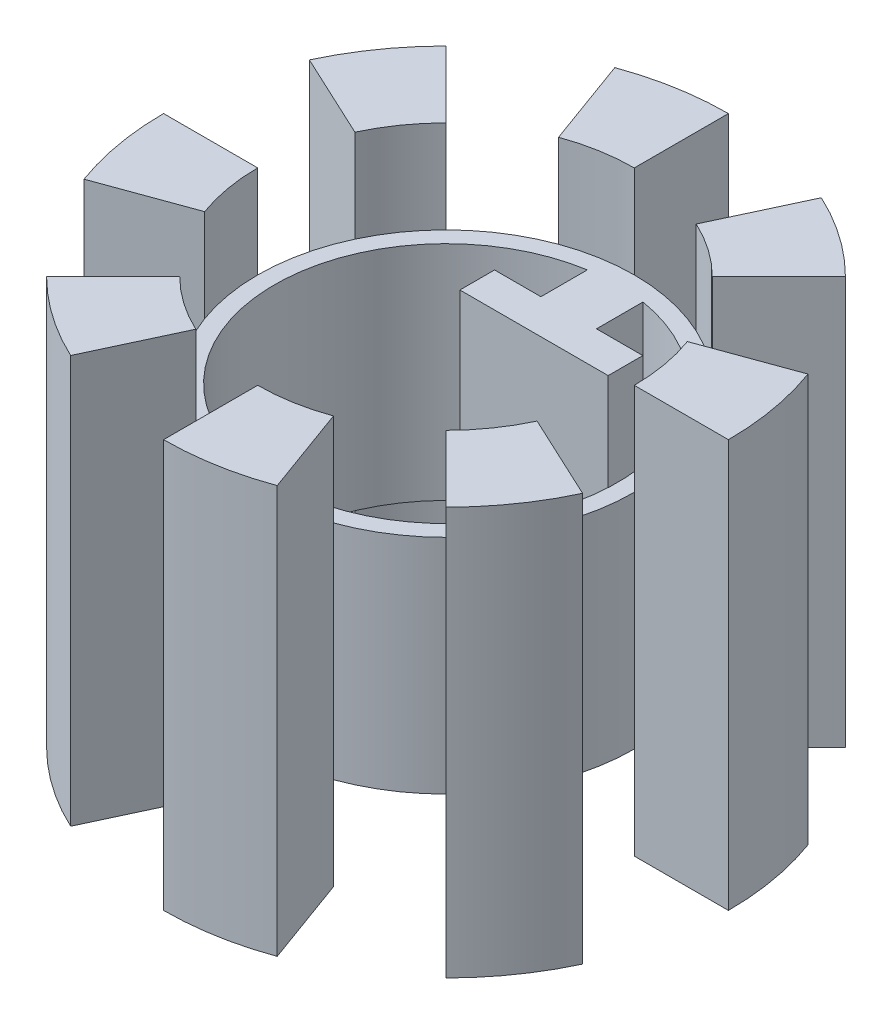
SolidWorks part; units mm, degrees
ref_plane "Front Plane" through (0, 0, 0) normal (0, 0, 1) x (1, 0, 0)
ref_plane "Top Plane" through (0, 0, 0) normal (0, 1, 0) x (1, 0, 0)
ref_plane "Right Plane" through (0, 0, 0) normal (1, 0, 0) x (0, 0, -1)
sketch "Sketch1" plane through (0, 0, 0) normal (0, 1, 0) x (1, 0, 0)
  line L0 (0, 15.24) -> (0, 0) construction
  line L1 (0, 0) -> (-5.2124, 14.3209) construction
  line L2 (0, 15.24) -> (0, 10.16)
  line L3 (-5.2124, 14.3209) -> (-3.4749, 9.5473)
  circle A0 centre (0, 0) radius 9.25
  arc A1 (0, 15.24) -> (-5.2124, 14.3209) centre (0, 0) ccw
  arc A2 (0, 10.16) -> (-3.4749, 9.5473) centre (0, 0) ccw
  circle A3 centre (0, 0) radius 10.16
  dimension "D1" = 18.5
  dimension "D2" = 20
  dimension "D3" = 15.24
  dimension "D4" = 10.16
extrude "Boss-Extrude1" add sketch "Sketch1" along normal blind 12 contours A3 | A0
ref_plane "Plane1" through (0, 6, 0) normal (0, -1, 0) x (-1, 0, 0)
sketch "Sketch3" plane through (0, 6, 0) normal (0, -1, 0) x (-1, 0, 0)
  line L0 (5.2124, 14.3209) -> (3.4749, 9.5473) construction
  line L1 (0, 15.24) -> (0, 10.16) construction
  line L2 (5.2124, 14.3209) -> (3.4749, 9.5473)
  line L3 (0, 15.24) -> (0, 10.16)
  line L4 (10.7763, 10.7763) -> (7.1842, 7.1842)
  line L5 (13.8121, 6.4407) -> (9.2081, 4.2938)
  line L6 (15.24, 0) -> (10.16, 0)
  line L7 (14.3209, -5.2124) -> (9.5473, -3.4749)
  line L8 (10.7763, -10.7763) -> (7.1842, -7.1842)
  line L9 (6.4407, -13.8121) -> (4.2938, -9.2081)
  line L10 (0, -15.24) -> (0, -10.16)
  line L11 (-5.2124, -14.3209) -> (-3.4749, -9.5473)
  line L12 (-10.7763, -10.7763) -> (-7.1842, -7.1842)
  line L13 (-13.8121, -6.4407) -> (-9.2081, -4.2938)
  line L14 (-15.24, 0) -> (-10.16, 0)
  line L15 (-14.3209, 5.2124) -> (-9.5473, 3.4749)
  line L16 (-10.7763, 10.7763) -> (-7.1842, 7.1842)
  line L17 (-6.4407, 13.8121) -> (-4.2938, 9.2081)
  line L18 (-15.24, 0) -> (0, 0) construction
  line L19 (0, 0) -> (-14.1828, 4.8835) construction
  line L20 (0, 0) -> (-15.0085, 2.6464) construction
  line L21 (-14.9977, 0.2618) -> (0, 0) construction
  line L22 (-14.9977, 0.2618) -> (-10.1585, 0.1773) construction
  line L23 (-14.1828, 4.8835) -> (-9.6065, 3.3078) construction
  line L24 (-6.5756, 13.4819) -> (-4.4539, 9.1317) construction
  line L25 (-10.4199, 10.7901) -> (-7.0577, 7.3085) construction
  line L26 (4.8835, 14.1828) -> (3.3078, 9.6065) construction
  line L27 (0.2618, 14.9977) -> (0.1773, 10.1585) construction
  line L28 (13.4819, 6.5756) -> (9.1317, 4.4539) construction
  line L29 (10.7901, 10.4199) -> (7.3085, 7.0577) construction
  line L30 (14.1828, -4.8835) -> (9.6065, -3.3078) construction
  line L31 (14.9977, -0.2618) -> (10.1585, -0.1773) construction
  line L32 (6.5756, -13.4819) -> (4.4539, -9.1317) construction
  line L33 (10.4199, -10.7901) -> (7.0577, -7.3085) construction
  line L34 (-4.8835, -14.1828) -> (-3.3078, -9.6065) construction
  line L35 (-0.2618, -14.9977) -> (-0.1773, -10.1585) construction
  line L36 (-13.4819, -6.5756) -> (-9.1317, -4.4539) construction
  line L37 (-10.7901, -10.4199) -> (-7.3085, -7.0577) construction
  arc A0 (3.4749, 9.5473) -> (0, 10.16) centre (0, 0) ccw construction
  arc A1 (5.2124, 14.3209) -> (0, 15.24) centre (0, 0) ccw construction
  arc A2 (3.4749, 9.5473) -> (0, 10.16) centre (0, 0) ccw
  arc A3 (5.2124, 14.3209) -> (0, 15.24) centre (0, 0) ccw
  arc A4 (9.2081, 4.2938) -> (7.1842, 7.1842) centre (0, 0) ccw
  arc A5 (13.8121, 6.4407) -> (10.7763, 10.7763) centre (0, 0) ccw
  arc A6 (9.5473, -3.4749) -> (10.16, 0) centre (0, 0) ccw
  arc A7 (14.3209, -5.2124) -> (15.24, 0) centre (0, 0) ccw
  arc A8 (4.2938, -9.2081) -> (7.1842, -7.1842) centre (0, 0) ccw
  arc A9 (6.4407, -13.8121) -> (10.7763, -10.7763) centre (0, 0) ccw
  arc A10 (-3.4749, -9.5473) -> (0, -10.16) centre (0, 0) ccw
  arc A11 (-5.2124, -14.3209) -> (0, -15.24) centre (0, 0) ccw
  arc A12 (-9.2081, -4.2938) -> (-7.1842, -7.1842) centre (0, 0) ccw
  arc A13 (-13.8121, -6.4407) -> (-10.7763, -10.7763) centre (0, 0) ccw
  arc A14 (-9.5473, 3.4749) -> (-10.16, 0) centre (0, 0) ccw
  arc A15 (-14.3209, 5.2124) -> (-15.24, 0) centre (0, 0) ccw
  arc A16 (-4.2938, 9.2081) -> (-7.1842, 7.1842) centre (0, 0) ccw
  arc A17 (-6.4407, 13.8121) -> (-10.7763, 10.7763) centre (0, 0) ccw
  arc A18 (-14.1828, 4.8835) -> (-14.9977, 0.2618) centre (0, 0) ccw construction
  circle A19 centre (0, 0) radius 10.16 construction
  arc A20 (-9.6065, 3.3078) -> (-10.1585, 0.1773) centre (0, 0) ccw construction
  arc A21 (-4.4539, 9.1317) -> (-7.0577, 7.3085) centre (0, 0) ccw construction
  arc A22 (-6.5756, 13.4819) -> (-10.4199, 10.7901) centre (0, 0) ccw construction
  arc A23 (3.3078, 9.6065) -> (0.1773, 10.1585) centre (0, 0) ccw construction
  arc A24 (4.8835, 14.1828) -> (0.2618, 14.9977) centre (0, 0) ccw construction
  arc A25 (9.1317, 4.4539) -> (7.3085, 7.0577) centre (0, 0) ccw construction
  arc A26 (13.4819, 6.5756) -> (10.7901, 10.4199) centre (0, 0) ccw construction
  arc A27 (9.6065, -3.3078) -> (10.1585, -0.1773) centre (0, 0) ccw construction
  arc A28 (14.1828, -4.8835) -> (14.9977, -0.2618) centre (0, 0) ccw construction
  arc A29 (4.4539, -9.1317) -> (7.0577, -7.3085) centre (0, 0) ccw construction
  arc A30 (6.5756, -13.4819) -> (10.4199, -10.7901) centre (0, 0) ccw construction
  arc A31 (-3.3078, -9.6065) -> (-0.1773, -10.1585) centre (0, 0) ccw construction
  arc A32 (-4.8835, -14.1828) -> (-0.2618, -14.9977) centre (0, 0) ccw construction
  arc A33 (-9.1317, -4.4539) -> (-7.3085, -7.0577) centre (0, 0) ccw construction
  arc A34 (-13.4819, -6.5756) -> (-10.7901, -10.4199) centre (0, 0) ccw construction
  point P36 (0, 0)
  point P39 (-14.7721, 2.6047)
  point P73 (0, 0)
  dimension "D2" = 18
  dimension "D3" = 15
  dimension "D1" = 8
  dimension "D4" = 8
extrude "Boss-Extrude3" add sketch "Sketch3" along normal mid plane 22
sketch "Sketch4" plane through (0, 0, 0) normal (0, -1, 0) x (1, 0, 0)
  line L0 (-0.2618, -14.9977) -> (-0.1773, -10.1585) construction
  line L1 (-3.3078, -9.6065) -> (-4.8835, -14.1828) construction
  line L2 (-0.2618, -14.9977) -> (-0.1773, -10.1585) construction
  line L3 (-3.3078, -9.6065) -> (-4.8835, -14.1828) construction
  line L4 (-3.3078, -8.6384) -> (-3.3078, -6.6384) construction
  line L5 (0, -9.25) -> (0, -6.6384) construction
  line L6 (-3.3078, -6.6384) -> (-5.1539, -6.6384) construction
  line L7 (-5.1539, -6.6384) -> (-5.1539, -4.8384) construction
  line L8 (-5.1539, -4.8384) -> (1.8461, -4.8384) construction
  line L9 (1.8461, -4.8384) -> (1.8461, -6.6384) construction
  line L10 (1.8461, -6.6384) -> (0, -6.6384) construction
  line L11 (-4, -6.6205) -> (-4, -4.75) construction
  line L12 (-4, -6.6205) -> (-1.5, -6.6205) construction
  line L13 (-1.5, -6.6205) -> (-1.5, -8.6205) construction
  line L14 (1.5, -6.6205) -> (1.5, -8.6205) construction
  line L15 (1.5, -6.6205) -> (4, -6.6205) construction
  line L16 (-4, -4.75) -> (4, -4.75) construction
  line L17 (4, -6.6205) -> (4, -4.75) construction
  line L18 (-4, -6.6205) -> (-4, -4.75)
  line L19 (-4, -6.6205) -> (-1.5, -6.6205)
  line L20 (-1.5, -6.6205) -> (-1.5, -8.6205)
  line L21 (1.5, -6.6205) -> (1.5, -8.6205)
  line L22 (1.5, -6.6205) -> (4, -6.6205)
  line L23 (-4, -4.75) -> (4, -4.75)
  line L24 (4, -6.6205) -> (4, -4.75)
  line L25 (-1.5, -8.6205) -> (-1.5, -9.1276)
  line L26 (1.5, -8.6205) -> (1.5, -9.1276)
  arc A0 (9.6065, -3.3078) -> (10.1585, -0.1773) centre (0, 0) ccw construction
  arc A1 (10.1585, -0.1773) -> (9.1317, 4.4539) centre (0, 0) ccw construction
  arc A2 (9.1317, 4.4539) -> (7.3085, 7.0577) centre (0, 0) ccw construction
  arc A3 (7.3085, 7.0577) -> (3.3078, 9.6065) centre (0, 0) ccw construction
  arc A4 (3.3078, 9.6065) -> (0.1773, 10.1585) centre (0, 0) ccw construction
  arc A5 (0.1773, 10.1585) -> (-4.4539, 9.1317) centre (0, 0) ccw construction
  arc A6 (-4.4539, 9.1317) -> (-7.0577, 7.3085) centre (0, 0) ccw construction
  arc A7 (-7.0577, 7.3085) -> (-9.6065, 3.3078) centre (0, 0) ccw construction
  arc A8 (-9.6065, 3.3078) -> (-10.1585, 0.1773) centre (0, 0) ccw construction
  arc A9 (-10.1585, 0.1773) -> (-9.1317, -4.4539) centre (0, 0) ccw construction
  arc A10 (-9.1317, -4.4539) -> (-7.3085, -7.0577) centre (0, 0) ccw construction
  arc A11 (-7.3085, -7.0577) -> (-3.3078, -9.6065) centre (0, 0) ccw construction
  arc A12 (-3.3078, -9.6065) -> (-0.1773, -10.1585) centre (0, 0) ccw construction
  arc A13 (-0.1773, -10.1585) -> (4.4539, -9.1317) centre (0, 0) ccw construction
  arc A14 (4.4539, -9.1317) -> (7.0577, -7.3085) centre (0, 0) ccw construction
  arc A15 (7.0577, -7.3085) -> (9.6065, -3.3078) centre (0, 0) ccw construction
  arc A16 (-4.8835, -14.1828) -> (-0.2618, -14.9977) centre (0, 0) ccw construction
  arc A17 (-3.3078, -9.6065) -> (-0.1773, -10.1585) centre (0, 0) ccw construction
  arc A18 (9.6065, -3.3078) -> (10.1585, -0.1773) centre (0, 0) ccw construction
  arc A19 (10.1585, -0.1773) -> (9.1317, 4.4539) centre (0, 0) ccw construction
  arc A20 (9.1317, 4.4539) -> (7.3085, 7.0577) centre (0, 0) ccw construction
  arc A21 (7.3085, 7.0577) -> (3.3078, 9.6065) centre (0, 0) ccw construction
  arc A22 (3.3078, 9.6065) -> (0.1773, 10.1585) centre (0, 0) ccw construction
  arc A23 (0.1773, 10.1585) -> (-4.4539, 9.1317) centre (0, 0) ccw construction
  arc A24 (-4.4539, 9.1317) -> (-7.0577, 7.3085) centre (0, 0) ccw construction
  arc A25 (-7.0577, 7.3085) -> (-9.6065, 3.3078) centre (0, 0) ccw construction
  arc A26 (-9.6065, 3.3078) -> (-10.1585, 0.1773) centre (0, 0) ccw construction
  arc A27 (-10.1585, 0.1773) -> (-9.1317, -4.4539) centre (0, 0) ccw construction
  arc A28 (-9.1317, -4.4539) -> (-7.3085, -7.0577) centre (0, 0) ccw construction
  arc A29 (-7.3085, -7.0577) -> (-3.3078, -9.6065) centre (0, 0) ccw construction
  arc A30 (-3.3078, -9.6065) -> (-0.1773, -10.1585) centre (0, 0) ccw construction
  arc A31 (-0.1773, -10.1585) -> (4.4539, -9.1317) centre (0, 0) ccw construction
  arc A32 (4.4539, -9.1317) -> (7.0577, -7.3085) centre (0, 0) ccw construction
  arc A33 (7.0577, -7.3085) -> (9.6065, -3.3078) centre (0, 0) ccw construction
  arc A34 (-4.8835, -14.1828) -> (-0.2618, -14.9977) centre (0, 0) ccw construction
  arc A35 (-3.3078, -9.6065) -> (-0.1773, -10.1585) centre (0, 0) ccw construction
  circle A36 centre (0, 0) radius 9.25 construction
  circle A37 centre (0, 0) radius 9.25 construction
  arc A38 (-3.3078, -8.6384) -> (0.0078, -9.25) centre (0, 0) ccw construction
  point P37 (0, -7.9442)
  dimension "D1" = 2
  dimension "D2" = 1.8
  dimension "D3" = 7
  dimension "D4" = 3.3078
extrude "Boss-Extrude4" add sketch "Sketch4" against normal up to surface (12 mm away) contours L10 L9 L8 L7 L6 L4 L5 M41 up to face at (0, 12, 0)
